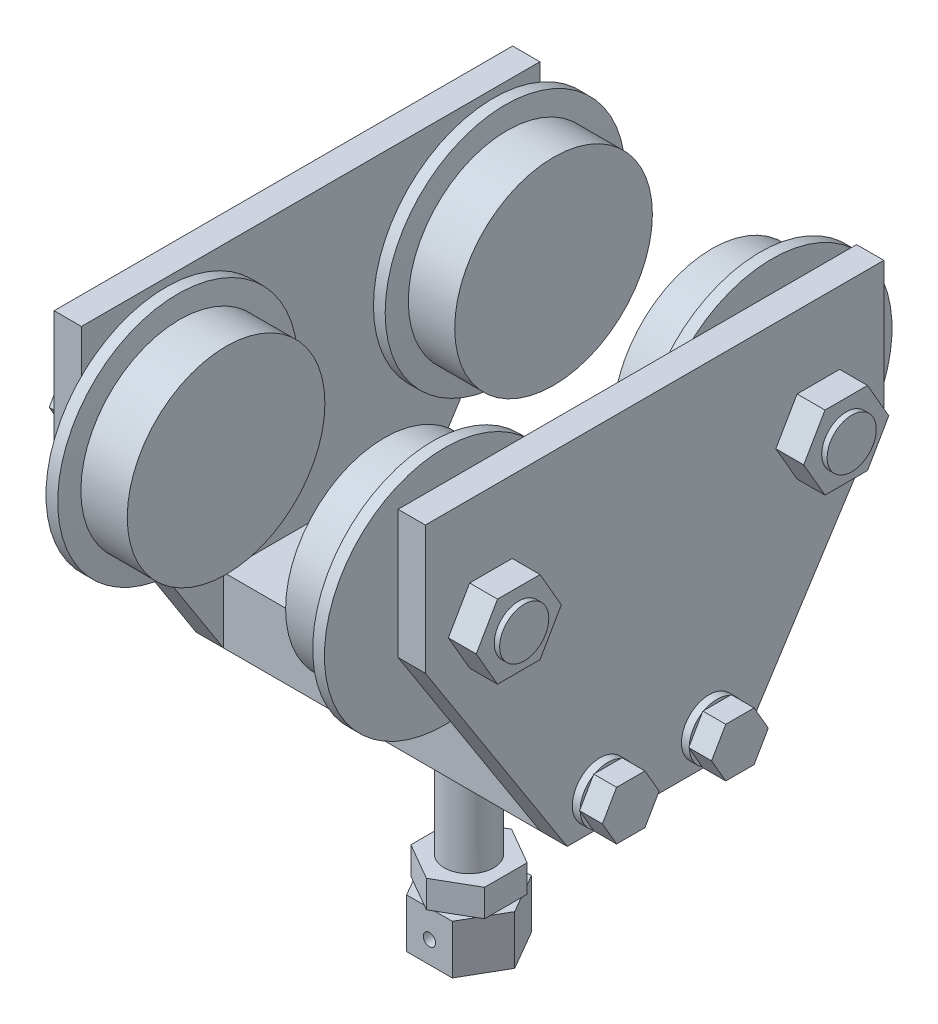
SolidWorks part; units mm, degrees
ref_plane "Front" through (0, 0, 0) normal (0, 0, 1) x (1, 0, 0)
ref_plane "Top" through (0, 0, 0) normal (0, 1, 0) x (1, 0, 0)
ref_plane "Right" through (0, 0, 0) normal (1, 0, 0) x (0, 0, -1)
ref_plane "Z PLANE" through (0, 0, 0) normal (0, 0, 1) x (1, 0, 0)
ref_plane "YOKE BOTTOM" through (0, 0, 0) normal (0, 1, 0) x (-1, 0, 0)
ref_plane "X PLANE" through (0, 0, 0) normal (1, 0, 0) x (0, 0, -1)
sketch "YOKE CROSS SECTION" plane through (0, 0, 0) normal (1, 0, 0) x (0, 0, -1)
  line L0 (0, 0) -> (0, 57.0916) construction
  line L1 (0, 84.8167) -> (0, -84.8167) construction
  line L2 (-50.8, 0) -> (50.8, 0)
  line L3 (69.1602, 0) -> (-69.1602, 0) construction
  line L4 (50.8, 0) -> (50.8, 38.1)
  line L5 (-50.8, 0) -> (-50.8, 38.1)
  line L6 (50.8, 38.1) -> (-50.8, 38.1)
  point P12 (0, 38.1)
  dimension "D1" = 38.1
  dimension "D2" = 101.6
ref_plane "1/2 YOKE LENGTH (A)" through (92.1015, 0, 0) normal (1, 0, 0) x (0, 0, -1)
ref_plane "WHEEL LOCATION" through (0, 0, 95.25) normal (0, 0, 1) x (1, 0, 0)
extrude "YOKE" add sketch "YOKE CROSS SECTION" along normal up to surface (92.1015 mm away) up to plane "1/2 YOKE LENGTH (A)"
sketch "SIDEPLATE PROFILE" plane through (92.1015, 0, 0) normal (1, 0, 0) x (0, 0, -1)
  line L0 (0, 0) -> (50.8, 0)
  line L1 (50.8, 0) -> (133.35, 128.5178)
  line L2 (133.35, 128.5178) -> (133.35, 203.2)
  line L3 (-133.35, 203.2) -> (133.35, 203.2)
  line L4 (-133.35, 128.5178) -> (-133.35, 203.2)
  line L5 (-50.8, 0) -> (-133.35, 128.5178)
  line L6 (0, 0) -> (-50.8, 0)
  line L7 (0, 84.8167) -> (0, -84.8167) construction
  line L8 (69.1602, 0) -> (-69.1602, 0) construction
  dimension "D1" = 50.8
  dimension "D2" = 50.8
  dimension "D3" = 82.55
  dimension "D4" = 82.55
  dimension "D5" = 128.5178
  dimension "D6" = 128.5178
  dimension "D7" = 74.6822
  dimension "D8" = 74.6822
  dimension "D9" = 266.7
ref_plane "WHEEL HEIGHT" through (0, 139.7, 0) normal (0, 1, 0) x (-1, 0, 0)
ref_plane "YOKE SCREW LOCATION Z" through (0, 0, 31.75) normal (0, 0, 1) x (1, 0, 0)
ref_plane "YOKE SCREW LOCATION Y" through (0, 19.05, 0) normal (0, 1, 0) x (-1, 0, 0)
extrude "SIDEPLATE" add sketch "SIDEPLATE PROFILE" along normal blind 15.875
sketch "WHEEL PIN NUT PROFILE" plane through (107.9765, 0, 0) normal (1, 0, 0) x (0, 0, -1)
  line L0 (-95.25, 84.8167) -> (-95.25, -84.8167) construction
  line L1 (-70.5033, 139.7) -> (-82.8767, 161.1312)
  line L2 (-82.8767, 161.1312) -> (-107.6233, 161.1312)
  line L3 (-107.6233, 161.1312) -> (-119.9967, 139.7)
  line L4 (-119.9967, 139.7) -> (-107.6233, 118.2688)
  line L5 (-107.6233, 118.2688) -> (-82.8767, 118.2688)
  line L6 (-82.8767, 118.2688) -> (-70.5033, 139.7)
  line L7 (69.1602, 139.7) -> (-69.1602, 139.7) construction
  circle A0 centre (-95.25, 139.7) radius 13.4938 construction
  dimension "D1" = 42.8625
extrude "WHEEL PIN NUT" add sketch "WHEEL PIN NUT PROFILE" along normal blind 16.2306
sketch "WHEEL PIN PROJECTION PROFILE" plane through (124.2071, 0, 0) normal (1, 0, 0) x (0, 0, -1)
  line L0 (-95.25, 84.8167) -> (-95.25, -84.8167) construction
  line L3 (69.1602, 139.7) -> (-69.1602, 139.7) construction
  circle A0 centre (-95.25, 139.7) radius 14.2875
  dimension "D1" = 28.575
extrude "WHEEL PIN PROJECTION" add sketch "WHEEL PIN PROJECTION PROFILE" along normal blind 3.175
sketch "LOCKNUTS PROFILE" plane through (107.9765, 0, 0) normal (1, 0, 0) x (0, 0, -1)
  line L0 (-31.75, 84.8167) -> (-31.75, -84.8167) construction
  line L1 (50, 19.05) -> (-50, 19.05) construction
  circle A0 centre (-31.75, 19.05) radius 16.129
  dimension "D1" = 32.258
extrude "LOCKNUTS" add sketch "LOCKNUTS PROFILE" along normal blind 4.572
sketch "SCREWS PROFILE" plane through (112.5485, 0, 0) normal (1, 0, 0) x (0, 0, -1)
  line L0 (50, 19.05) -> (-50, 19.05) construction
  line L1 (-15.2522, 19.05) -> (-23.5011, 33.3375)
  line L2 (-23.5011, 33.3375) -> (-39.9989, 33.3375)
  line L3 (-39.9989, 33.3375) -> (-48.2478, 19.05)
  line L4 (-48.2478, 19.05) -> (-39.9989, 4.7625)
  line L5 (-39.9989, 4.7625) -> (-23.5011, 4.7625)
  line L6 (-23.5011, 4.7625) -> (-15.2522, 19.05)
  line L7 (-31.75, 84.8167) -> (-31.75, -84.8167) construction
  circle A0 centre (-31.75, 19.05) radius 14.2875 construction
  dimension "D1" = 28.575
extrude "SCREWS" add sketch "SCREWS PROFILE" along normal blind 13.3096
sketch "PROFILE" plane through (0, 38.1, 0) normal (0, 1, 0) x (-1, 0, 0)
  line L0 (84.8167, 0) -> (-84.8167, 0) construction
  line L1 (0, 83.2389) -> (0, -83.2389) construction
  circle A0 centre (0, 0) radius 22.225
  dimension "D1" = 44.45
extrude "KING BOLT HEAD" add sketch "PROFILE" along normal blind 25.4
mirror "Mirror1" about plane through (0, 0, 0) normal (0, 0, 1) of "WHEEL PIN PROJECTION", "WHEEL PIN NUT"
mirror "Mirror YOKE SCREWS" about plane through (0, 0, 0) normal (0, 0, 1) of "SCREWS", "LOCKNUTS"
mirror "Mirror SIDE 1" about plane through (0, 0, 0) normal (1, 0, 0) of bodies 112
ref_plane "TOP OF NUT" through (0, -83.0521, 0) normal (0, 1, 0) x (-1, 0, 0)
sketch "DIA." plane through (0, 0, 0) normal (0, -1, 0) x (1, 0, 0)
  line L0 (84.8167, 0) -> (-84.8167, 0) construction
  line L1 (0, -83.2389) -> (0, 83.2389) construction
  circle A0 centre (0, 0) radius 14.2875
  dimension "D1" = 28.575
extrude "KING BOLT" add sketch "DIA." along normal up to surface (83.0521 mm away) up to plane "TOP OF NUT"
sketch "KING BOLT JAN NUT PROFILE" plane through (0, -83.0521, 0) normal (0, -1, 0) x (1, 0, 0)
  line L0 (84.8167, 0) -> (-84.8167, 0) construction
  line L1 (0, -24.754) -> (21.4376, -12.377)
  line L2 (21.4376, -12.377) -> (21.4376, 12.377)
  line L3 (21.4376, 12.377) -> (0, 24.754)
  line L4 (0, 24.754) -> (-21.4376, 12.377)
  line L5 (-21.4376, 12.377) -> (-21.4376, -12.377)
  line L6 (-21.4376, -12.377) -> (0, -24.754)
  line L7 (0, -83.2389) -> (0, 83.2389) construction
  circle A0 centre (0, 0) radius 21.4376 construction
  dimension "D1" = 42.8752
extrude "KING BOLT JAM NUT" add sketch "KING BOLT JAN NUT PROFILE" along normal blind 15.875
sketch "KING BOLT NUT PROFILE" plane through (0, -98.9271, 0) normal (0, -1, 0) x (1, 0, 0)
  line L1 (26.5798, 0) -> (13.2899, 23.0188)
  line L2 (13.2899, 23.0188) -> (-13.2899, 23.0188)
  line L3 (-13.2899, 23.0188) -> (-26.5798, 0)
  line L4 (-26.5798, 0) -> (-13.2899, -23.0187)
  line L5 (-13.2899, -23.0187) -> (13.2899, -23.0187)
  line L6 (13.2899, -23.0187) -> (26.5798, 0)
  line L10 (0, -83.2389) -> (0, 83.2389) construction
  line L11 (84.8167, 0) -> (-84.8167, 0) construction
  circle A0 centre (0, 0) radius 23.0188 construction
  dimension "D1" = 46.0375
extrude "KING BOLT NUT" add sketch "KING BOLT NUT PROFILE" along normal blind 28.575
sketch "Sketch5" plane through (0, -127.5021, 0) normal (0, -1, 0) x (1, 0, 0)
  circle A0 centre (0, 0) radius 14.2875 construction
  circle A1 centre (0, 0) radius 14.2875
extrude "EXTENDED KING BOLT" add sketch "Sketch5" along normal blind 6.35
chamfer "Chamfer1" distance 2.3812 angle 45 1 edges at (0, -133.8521, -14.2875)
ref_plane "MOUNTING REF PLANE" through (0, -34.925, 0) normal (0, 1, 0) x (-1, 0, 0)
sketch "Sketch6" plane through (0, 0, 95.25) normal (0, 0, 1) x (1, 0, 0)
  line L0 (92.1015, 158.75) -> (92.1015, 139.7)
  line L1 (46.064, 139.7) -> (46.064, 197.1958)
  line L2 (92.1015, 139.7) -> (92.1015, 158.75)
  line L3 (46.064, 139.7) -> (92.1015, 139.7)
  line L4 (80.989, 158.75) -> (80.989, 209.55)
  line L5 (80.989, 158.75) -> (92.1015, 158.75)
  line L6 (73.0515, 197.1958) -> (74.1626, 209.55)
  line L7 (74.1626, 209.55) -> (80.989, 209.55)
  line L8 (113.7467, 139.7) -> (-113.7467, 139.7) construction
  line L9 (92.1015, -75.0522) -> (92.1015, 75.0522) construction
  line L10 (73.0515, 197.1958) -> (46.064, 197.1958)
  dimension "D11" = 46.0375
  dimension "D1" = 11.1125
  dimension "D2" = 17.9389
  dimension "D3" = 19.05
  dimension "D4" = 46.0375
  dimension "D5" = 19.05
  dimension "D6" = 57.4958
  dimension "D8" = 69.85
  dimension "D9" = 69.85
revolve "WHEEL" add sketch "Sketch6" angle 360 about axis through (127.3821, 139.7, 95.25) along (-1, 0, 0)
mirror "Mirror2" about plane through (0, 0, 0) normal (0, 0, 1) of "WHEEL"
mirror "Mirror3" about plane through (0, 0, 0) normal (1, 0, 0) of "Mirror2", "WHEEL"
sketch "Sketch7" plane through (0, 0, 23.0188) normal (0, 0, 1) x (1, 0, 0)
  line L0 (0, -83.2389) -> (0, 83.2389) construction
  line L1 (-13.2899, -127.5021) -> (-26.5798, -127.5021) construction
  circle A0 centre (0, -114.8021) radius 3.5719
  point P4 (-19.9348, -127.5021)
  dimension "D2" = 7.1437
  dimension "D1" = 12.7
extrude "COTTER PIN HOLE" cut sketch "Sketch7" against normal up to next
sketch "Sketch8" plane through (0, 0, 0) normal (0, -1, 0) x (1, 0, 0)
  circle A0 centre (0, 0) radius 25.4
  circle A1 centre (0, 0) radius 30.1625
  dimension "D1" = 50.8
  dimension "D2" = 60.325
extrude "SPACER" [suppressed] add sketch "Sketch8" along normal blind 12.7
ref_plane "TREAD OF TRACK" through (0, 82.55, 0) normal (0, 1, 0) x (-1, 0, 0)
